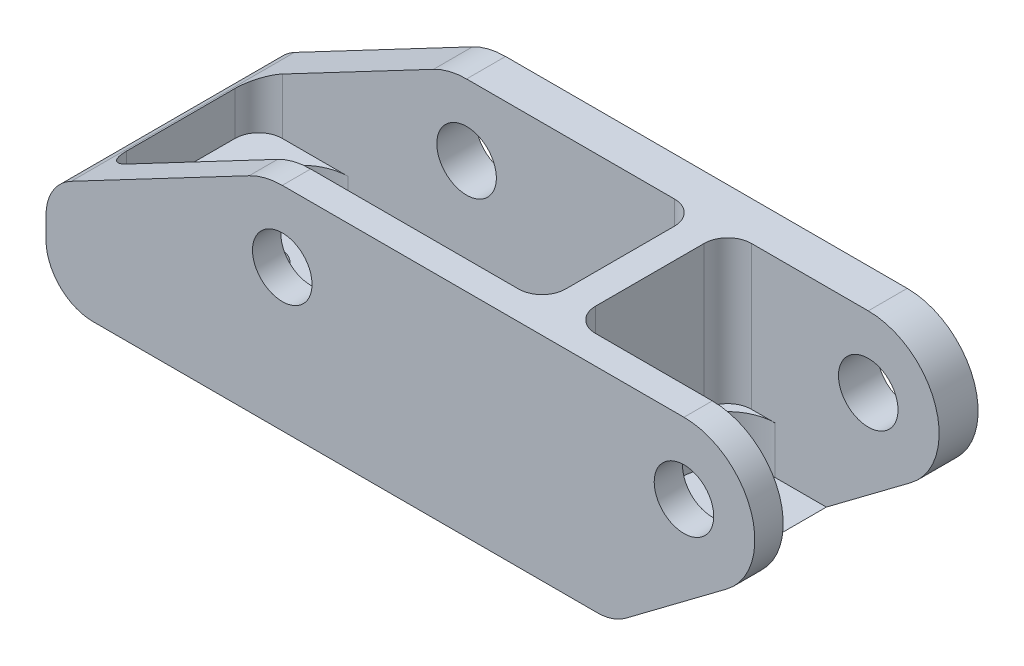
SolidWorks part; units mm, degrees
ref_plane "Front Plane" through (0, 0, 0) normal (0, 0, 1) x (1, 0, 0)
ref_plane "Top Plane" through (0, 0, 0) normal (0, 1, 0) x (1, 0, 0)
ref_plane "Right Plane" through (0, 0, 0) normal (1, 0, 0) x (0, 0, -1)
sketch "Sketch1" plane through (0, 0, 0) normal (0, 1, 0) x (1, 0, 0)
  line L0 (0, 6.6667) -> (0, 23.3333)
  line L1 (6.6667, 30) -> (93.3333, 30)
  line L3 (93.3333, 0) -> (6.6667, 0)
  line L4 (93.3333, 30) -> (100, 30)
  line L5 (100, 30) -> (100, 0)
  line L6 (100, 0) -> (93.3333, 0)
  line L7 (6.6667, 30) -> (0, 30)
  line L8 (0, 30) -> (0, 23.3333)
  line L9 (6.6667, 0) -> (0, 0)
  line L10 (0, 0) -> (0, 6.6667)
  circle A0 centre (13.3333, 15) radius 3.1496
  circle A1 centre (53.3333, 15) radius 3.1496
  point P0 (0, 0)
  point P1 (0, 30)
  point P2 (100, 30)
  point P3 (100, 0)
  point P4 (0, 0)
  point P6 (13.3333, 15)
  point P9 (53.3333, 15)
  dimension "D1" = 40
extrude "Boss-Extrude1" add sketch "Sketch1" against normal blind 28.575
sketch "Sketch2" plane through (0, 0, 0) normal (0, 1, 0) x (1, 0, 0)
  line L15 (3.81, 6.985) -> (3.81, 21.59)
  line L16 (6.985, 24.765) -> (59.6783, 24.765)
  line L17 (62.8533, 21.59) -> (62.8533, 6.985)
  line L18 (59.6783, 3.81) -> (6.985, 3.81)
  line L19 (66.8533, 6.985) -> (66.8533, 21.59)
  line L20 (70.0283, 24.765) -> (95.25, 24.765)
  line L21 (95.25, 24.765) -> (95.25, 3.81)
  line L22 (95.25, 3.81) -> (70.0283, 3.81)
  line L24 (0, 0) -> (100, 0) construction
  arc A10 (59.6783, 3.81) -> (62.8533, 6.985) centre (59.6783, 6.985) ccw
  arc A11 (62.8533, 21.59) -> (59.6783, 24.765) centre (59.6783, 21.59) ccw
  arc A12 (6.985, 24.765) -> (3.81, 21.59) centre (6.985, 21.59) ccw
  arc A13 (3.81, 6.985) -> (6.985, 3.81) centre (6.985, 6.985) ccw
  arc A14 (70.0283, 24.765) -> (66.8533, 21.59) centre (70.0283, 21.59) ccw
  arc A15 (66.8533, 6.985) -> (70.0283, 3.81) centre (70.0283, 6.985) ccw
  circle A16 centre (13.3333, 15) radius 3.1496 construction
  circle A17 centre (53.3333, 15) radius 3.1496 construction
  point P0 (5.08, 5.08)
  point P1 (5.08, 23.368)
  point P2 (58.42, 23.368)
  point P3 (58.42, 5.08)
  point P16 (63.5, 23.368)
  point P17 (63.5, 5.08)
  point P18 (95.25, 23.368)
  point P19 (95.25, 5.08)
  point P21 (3.81, 3.81)
  point P25 (3.81, 24.765)
  point P26 (59.69, 24.765)
  point P27 (59.69, 3.81)
  point P28 (63.5, 24.765)
  point P29 (63.5, 3.81)
  point P30 (95.25, 24.765)
  point P31 (95.25, 3.81)
  point P40 (62.8533, 14.2875)
  point P41 (0, 0)
  point P45 (0, 0)
  point P46 (0, 0)
  point P47 (0, 0)
  point P48 (0, 0)
  point P49 (0, 0)
  point P50 (0, 0)
  point P51 (0, 0)
  point P52 (0, 0)
  point P53 (0, 0)
  point P54 (6.8621, 24.3751)
  point P55 (0, 0)
  point P56 (0, 0)
  point P57 (0, 0)
  point P58 (-100.5647, 45.3573)
  point P59 (-63.1437, 40.1508)
  dimension "D1" = 3.175
  dimension "D2" = 3.175
  dimension "D3" = 9.5233
  dimension "D4" = 9.52
  dimension "D5" = 4
  dimension "D6" = 52.6933
  dimension "D7" = 25.2217
  dimension "D8" = 20.955
  dimension "D9" = 14.605
  dimension "D10" = 25.2217
extrude "Cut-Extrude1" cut sketch "Sketch2" against normal blind 19.304
sketch "Sketch9" plane through (0, -19.304, 0) normal (0, 1, 0) x (1, 0, 0)
  line L0 (7.6491, 18.136) -> (10.794, 22.2635)
  line L1 (15.8449, 24.765) -> (50.8184, 24.765)
  line L2 (7.6491, 10.439) -> (10.794, 6.3115)
  line L3 (15.8449, 3.81) -> (50.8184, 3.81)
  line L6 (66.8533, 18.415) -> (66.8533, 10.16)
  line L7 (73.2033, 3.81) -> (95.25, 3.81)
  line L8 (95.25, 3.81) -> (95.25, 24.765)
  line L9 (95.25, 24.765) -> (73.2033, 24.765)
  line L10 (66.8533, 21.59) -> (66.8533, 6.985) construction
  line L11 (95.25, 3.81) -> (95.25, 24.765) construction
  line L12 (6.35, 14.2875) -> (57.15, 14.2875) construction
  line L13 (33.3317, 14.2875) -> (33.3317, -8.6228) construction
  line L14 (33.3317, -8.6228) -> (33.3317, 34.6872) construction
  line L16 (3.81, 21.59) -> (3.81, 6.985) construction
  line L17 (59.6783, 24.765) -> (6.985, 24.765) construction
  line L18 (59.0142, 10.439) -> (55.8693, 6.3115)
  line L19 (59.0142, 18.136) -> (55.8693, 22.2635)
  line L20 (59.6783, 24.765) -> (6.985, 24.765) construction
  arc A0 (7.6491, 18.136) -> (7.6491, 10.439) centre (12.7, 14.2875) ccw
  arc A2 (15.8449, 24.765) -> (10.794, 22.2635) centre (15.8449, 18.415) ccw
  arc A3 (10.794, 6.3115) -> (15.8449, 3.81) centre (15.8449, 10.16) ccw
  arc A6 (66.8533, 10.16) -> (73.2033, 3.81) centre (73.2033, 10.16) ccw
  arc A7 (66.8533, 18.415) -> (73.2033, 24.765) centre (73.2033, 18.415) cw
  arc A8 (55.8693, 6.3115) -> (50.8184, 3.81) centre (50.8184, 10.16) cw
  arc A9 (59.0142, 18.136) -> (59.0142, 10.439) centre (53.9633, 14.2875) cw
  arc A10 (50.8184, 24.765) -> (55.8693, 22.2635) centre (50.8184, 18.415) cw
  point P0 (12.7, 14.2875)
  point P1 (50.8, 14.2875)
  point P3 (63.5, 24.765)
  point P4 (0, 0)
  point P5 (95.25, 24.765)
  point P6 (12.7, 24.765)
  point P7 (12.7, 3.81)
  point P8 (50.8, 24.765)
  point P9 (50.8, 3.81)
  point P13 (0, 0)
  point P15 (0, 0)
  point P18 (95.25, 3.81)
  point P19 (63.5, 3.81)
  point P20 (63.5, 24.765)
  point P50 (0, 0)
  point P51 (33.3317, 24.765)
  dimension "D1" = 6.35
  dimension "D2" = 8.89
extrude "Cut-Extrude7" cut sketch "Sketch9" against normal blind 6.35
sketch "Sketch5" plane through (0, 0, -30) normal (0, 0, -1) x (-1, 0, 0)
  line L0 (-91.44, -17.145) -> (-77.8933, -27.305)
  line L1 (-74.0833, -28.575) -> (-100, -28.575)
  line L2 (-100, -28.575) -> (-100, 0)
  line L3 (-100, 0) -> (-85.725, 0)
  line L4 (-27.3084, -1.099) -> (-3.3889, -13.7076)
  line L5 (0, -19.3249) -> (0, -22.225)
  line L6 (-100, -28.575) -> (-100, 0) construction
  line L7 (-31.75, 0) -> (0, 0)
  line L8 (0, 0) -> (0, -19.3249)
  line L9 (0, -22.225) -> (0, -28.575)
  line L10 (0, -28.575) -> (-6.35, -28.575)
  line L11 (-100, 0) -> (0, 0) construction
  circle A0 centre (-31.75, -9.525) radius 4
  circle A1 centre (-85.725, -9.525) radius 4
  arc A3 (-85.725, 0) -> (-91.44, -17.145) centre (-85.725, -9.525) ccw
  arc A4 (-77.8933, -27.305) -> (-74.0833, -28.575) centre (-74.0833, -22.225) ccw
  arc A5 (-27.3084, -1.099) -> (-31.75, 0) centre (-31.75, -9.525) ccw
  arc A6 (0, -22.225) -> (-6.35, -28.575) centre (-6.35, -22.225) cw
  arc A7 (0, -19.3249) -> (-3.3889, -13.7076) centre (-6.35, -19.3249) ccw
  point P0 (-31.75, -9.525)
  point P1 (-85.725, -9.525)
  point P6 (-76.2, -28.575)
  point P11 (0, -15.494)
  point P30 (0, 0)
  point P31 (0, 0)
  point P32 (0, 0)
  point P33 (0, 0)
  line M3 (0, 0) -> (-100, 0)
  line M4 (-100, 0) -> (-100, -28.575)
  line M5 (-100, -28.575) -> (0, -28.575)
  line M23 (0, -28.575) -> (0, 0)
  dimension "D1" = 6.35
  dimension "D2" = 6.35
extrude "Cut-Extrude3" cut sketch "Sketch5" against normal through all contours A7 A5 L4 M23 M3 | A6 M23 M5 | A4 L0 A3 M3 M4 M5 | A1 | A0
